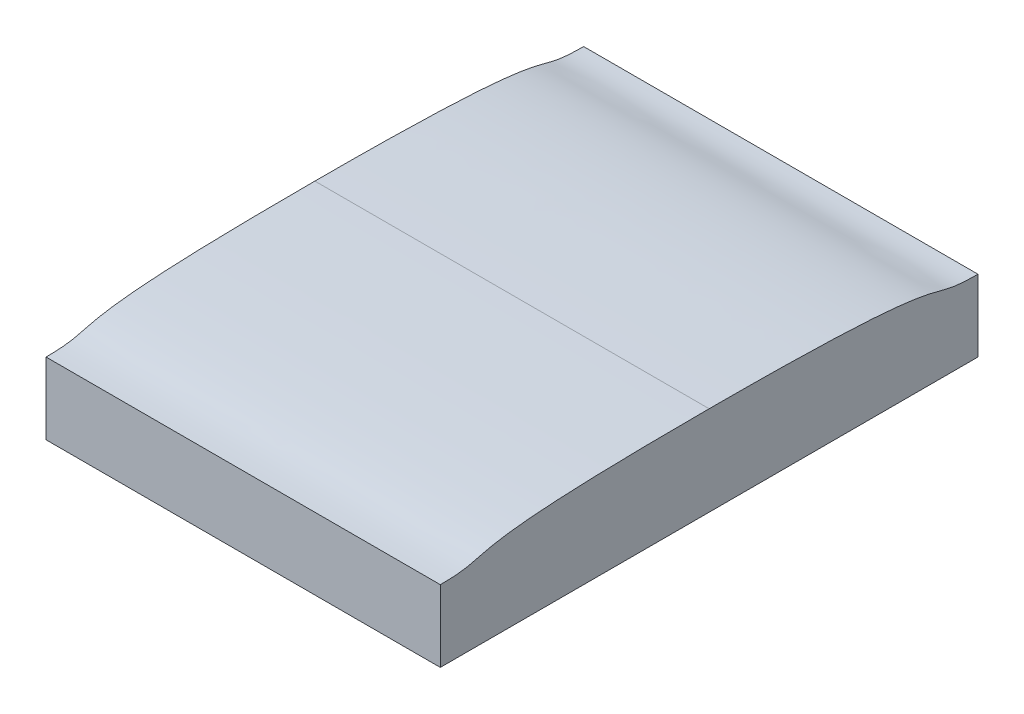
SolidWorks part; units mm, degrees
ref_plane "Front Plane" through (0, 0, 0) normal (0, 0, 1) x (1, 0, 0)
ref_plane "Top Plane" through (0, 0, 0) normal (0, 1, 0) x (1, 0, 0)
ref_plane "Right Plane" through (0, 0, 0) normal (1, 0, 0) x (0, 0, -1)
sketch "Sketch1" plane through (0, 0, 0) normal (1, 0, 0) x (0, 0, -1)
  line L0 (0, 0) -> (0, 10.6913) construction
  line L1 (15, -0.2307) -> (15, 3.7693)
  line L2 (-4.8433, -0.2307) -> (4.8433, -0.2307) construction
  line L3 (-3.6834, 4.7693) -> (3.6834, 4.7693) construction
  line L4 (12.153, 3.7693) -> (18.5837, 3.7693) construction
  line L5 (-15, -0.2307) -> (-15, 3.7693)
  spline S0 degree 3 poles (15, -0.2307) (10.3899, -0.2307) (8.6691, -0.2307) (0, -0.2307) knots 0 0 0 0 1 1 1 1
  spline S1 degree 3 poles (15, 3.7693) (11.4835, 3.7693) (14.9525, 4.7693) (0, 4.7693) knots 0 0 0 0 1 1 1 1
  spline S2 degree 3 poles (-15, -0.2307) (-10.3899, -0.2307) (-8.6691, -0.2307) (0, -0.2307) knots 0 0 0 0 1 1 1 1
  spline S3 degree 3 poles (-15, 3.7693) (-11.4835, 3.7693) (-14.9525, 4.7693) (0, 4.7693) knots 0 0 0 0 1 1 1 1
  point P13 (15, 1.7693)
  point P16 (-15, 1.7693)
  dimension "D1" = 4
  dimension "D2" = 0
  dimension "D3" = 0
  dimension "D4" = 30
  dimension "D5" = 5
extrude "Boss-Extrude1" add sketch "Sketch1" along normal blind 22
